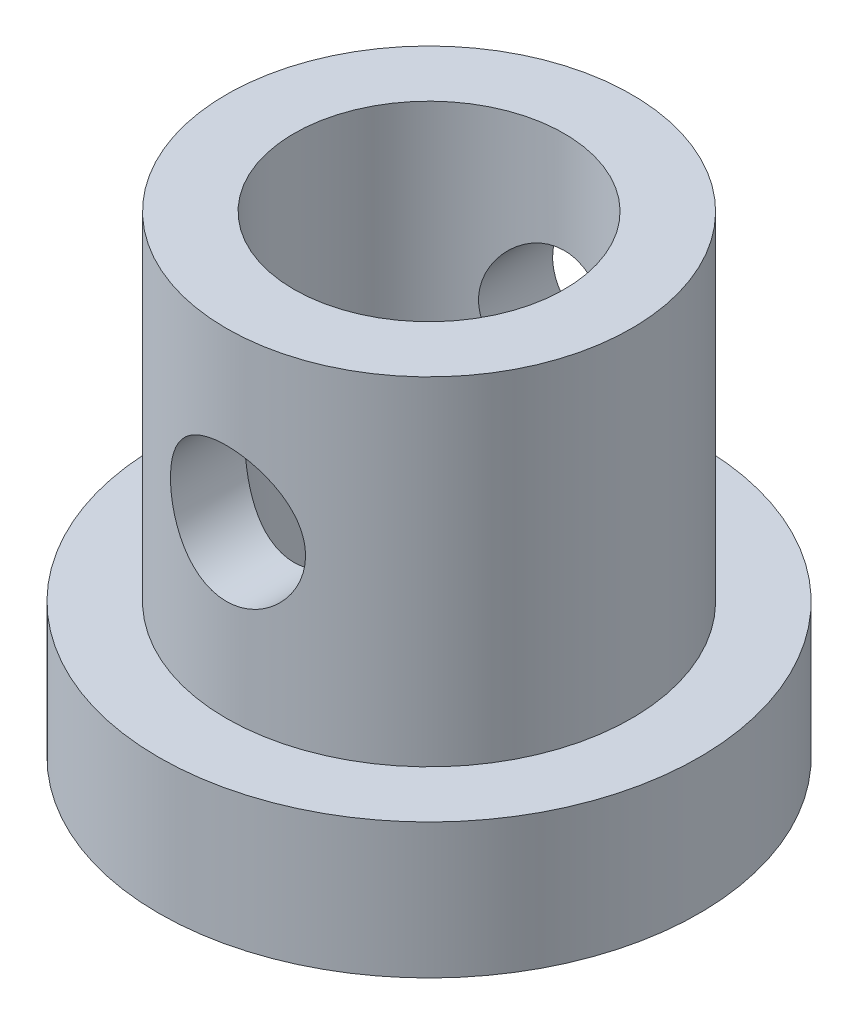
SolidWorks part; units mm, degrees
ref_plane "Front Plane" through (0, 0, 0) normal (0, 0, 1) x (1, 0, 0)
ref_plane "Top Plane" through (0, 0, 0) normal (0, 1, 0) x (1, 0, 0)
ref_plane "Right Plane" through (0, 0, 0) normal (1, 0, 0) x (0, 0, -1)
sketch "Sketch2" plane through (0, 0, 0) normal (0, 1, 0) x (1, 0, 0)
  circle A0 centre (0, 0) radius 4
  circle A1 centre (0, 0) radius 2
extrude "Boss-Extrude1" add sketch "Sketch2" along normal blind 2
sketch "Sketch3" plane through (0, 2, 0) normal (0, 1, 0) x (1, 0, 0)
  circle A0 centre (0, 0) radius 3
  circle A1 centre (0, 0) radius 2
extrude "Boss-Extrude2" add sketch "Sketch3" along normal blind 5
sketch "Sketch4" plane through (0, 0, 0) normal (0, 0, 1) x (1, 0, 0)
  line L0 (3, 7) -> (-3, 7) construction
  circle A0 centre (0, 4.5) radius 1
  dimension "D1" = 2.5
extrude "Cut-Extrude1" cut sketch "Sketch4" against normal through all both and the other way through all
